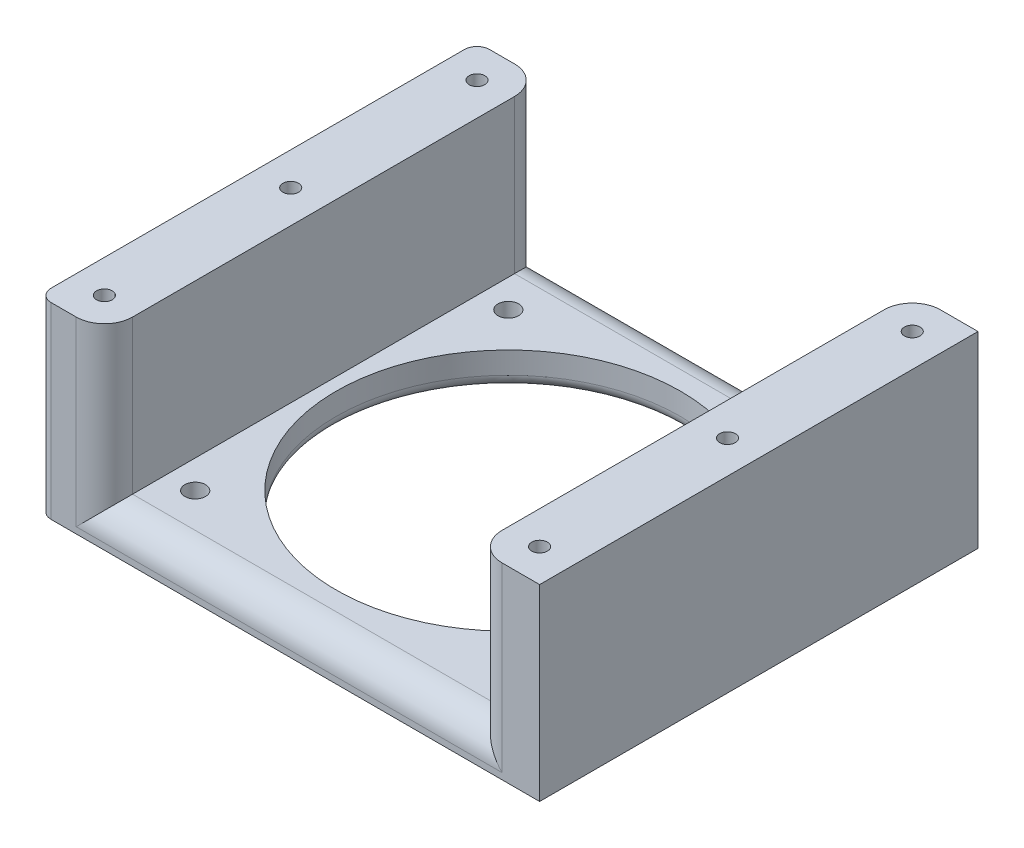
SolidWorks part; units mm, degrees
ref_plane "Front Plane" through (0, 0, 0) normal (0, 0, 1) x (1, 0, 0)
ref_plane "Top Plane" through (0, 0, 0) normal (0, 1, 0) x (1, 0, 0)
ref_plane "Right Plane" through (0, 0, 0) normal (1, 0, 0) x (0, 0, -1)
sketch "Sketch1" plane through (0, 0, 0) normal (0, 1, 0) x (1, 0, 0)
  line L1 (-42.6313, 37.6028) -> (37.3687, 37.6028)
  line L2 (-42.6313, 37.6028) -> (-42.6313, -32.3972)
  line L3 (-42.6313, -32.3972) -> (37.3687, -32.3972)
  line L4 (37.3687, 37.6028) -> (37.3687, -32.3972)
  dimension "D1" = 80
  dimension "D2" = 70
extrude "Boss-Extrude1" add sketch "Sketch1" along normal blind 35.5
sketch "Sketch2" plane through (0, 0, 32.3972) normal (0, 0, 1) x (1, 0, 0)
  line L0 (-42.6313, 35.5) -> (37.3687, 35.5) construction
  line L1 (-32.1313, 30) -> (26.8687, 30)
  line L2 (-32.1313, 30) -> (-32.1313, 5.5)
  line L3 (-32.1313, 5.5) -> (26.8687, 5.5)
  line L4 (26.8687, 30) -> (26.8687, 5.5)
  line L5 (-42.6313, 35.5) -> (-42.6313, 0) construction
  dimension "D1" = 59
  dimension "D2" = 24.5
  dimension "D3" = 5.5
  dimension "D4" = 10.5
extrude "Cut-Extrude1" cut sketch "Sketch2" against normal up to next
sketch "Sketch6" plane through (0, 0, 0) normal (0, -1, 0) x (1, 0, 0)
  line L0 (-42.6313, 32.3972) -> (37.3687, 32.3972) construction
  line L2 (-42.6313, -37.6028) -> (-42.6313, 32.3972) construction
  circle A0 centre (-2.6313, -2.6028) radius 27.5
  dimension "D3" = 55
  dimension "D1" = 35
  dimension "D2" = 40
extrude "Cut-Extrude3" cut sketch "Sketch6" against normal blind 5.5
sketch "Sketch7" plane through (0, 0, 0) normal (0, -1, 0) x (1, 0, 0)
  line L0 (-42.6313, -37.6028) -> (-42.6313, 32.3972) construction
  line L1 (-42.6313, 32.3972) -> (37.3687, 32.3972) construction
  line L2 (37.3687, 32.3972) -> (37.3687, -37.6028) construction
  line L3 (37.3687, -37.6028) -> (-42.6313, -37.6028) construction
  point P0 (-27.6313, 22.3972)
  point P1 (22.3687, 22.3972)
  point P2 (22.3687, -27.6028)
  point P3 (-27.6313, -27.6028)
  dimension "D1" = 15
  dimension "D2" = 10
  dimension "D3" = 10
  dimension "D4" = 15
  dimension "D5" = 15
  dimension "D6" = 10
  dimension "D7" = 10
  dimension "D8" = 15
hole_wizard "M4x0.7 Tapped Hole1" positions "3DSketch2" profile "Sketch8" tap size "M4x0.7" standard "Ansi Metric" end condition up to next
sketch3d "3DSketch2"
  point P0 (22.3687, 0, 22.3972)
  point P3 (22.3687, 0, -27.6028)
  point P6 (-27.6313, 0, -27.6028)
  point P9 (-27.6313, 0, 22.3972)
sketch "Sketch8" plane through (22.3687, 0, 22.3972) normal (1, 0, 0) x (0, 0, -1)
  line L0 (0, 0) -> (0, 5.5)
  line L1 (0, 5.5) -> (1.65, 5.5)
  line L2 (1.65, 5.5) -> (1.65, 0)
  line L5 (1.65, 0) -> (0, 0)
  line L11 (0, -6.35) -> (0, 107.95) construction
  dimension "Thread Major Dia." = 3.3
  dimension "Thru Tap Drill Depth" = 5.5
fillet "Fillet2" radius 2 1 edges at (-2.6313, 0, -30.1028)
sketch "Sketch9" plane through (0, 35.5, 0) normal (0, 1, 0) x (-1, 0, 0)
  line L1 (42.6313, -37.6028) -> (-37.3687, -37.6028)
  line L2 (42.6313, -37.6028) -> (42.6313, 32.3972)
  line L3 (42.6313, 32.3972) -> (-37.3687, 32.3972)
  line L4 (-37.3687, -37.6028) -> (-37.3687, 32.3972)
extrude "Cut-Extrude5" cut sketch "Sketch9" against normal up to surface (5.5 mm away) up to face at (-2.6313, 30, -2.6028)
sketch "Sketch10" plane through (0, 30, 0) normal (0, 1, 0) x (1, 0, 0)
  line L0 (-42.6313, 37.6028) -> (-32.1313, 37.6028) construction
  line L1 (-42.6313, -32.3972) -> (-42.6313, 37.6028) construction
  line L2 (-32.1313, -32.3972) -> (-42.6313, -32.3972) construction
  line L3 (26.8687, 37.6028) -> (26.8687, -32.3972) construction
  line L4 (26.8687, 37.6028) -> (37.3687, 37.6028) construction
  line L5 (37.3687, -32.3972) -> (26.8687, -32.3972) construction
  point P0 (-37.3813, 32.3528)
  point P1 (-37.3813, 2.6028)
  point P2 (-37.3813, -27.1472)
  point P3 (-37.3813, 37.6028)
  point P12 (32.1187, 32.3528)
  point P13 (32.1187, 2.8528)
  point P14 (32.1187, -27.1472)
  dimension "D1" = 5.25
  dimension "D2" = 5.25
  dimension "D3" = 5.25
  dimension "D4" = 35
  dimension "D5" = 5.25
  dimension "D6" = 5.25
  dimension "D7" = 5.25
hole_wizard "Tap Drill for M3x0.5 Tap1" positions "3DSketch3" profile "Sketch11" hole size "M3x0.5" standard "Ansi Metric"
sketch3d "3DSketch3"
  point P0 (-37.3813, 30, -32.3528)
  point P3 (-37.3813, 30, -2.6028)
  point P6 (-37.3813, 30, 27.1472)
  point P9 (32.1187, 30, -32.3528)
  point P12 (32.1187, 30, -2.8528)
  point P15 (32.1187, 30, 27.1472)
sketch "Sketch11" plane through (-37.3813, 30, -32.3528) normal (1, 0, 0) x (0, 0, 1)
  line L0 (0, 0) -> (0, 15.7511)
  line L1 (0, 15.7511) -> (1.25, 15)
  line L2 (1.25, 15) -> (1.25, 0)
  line L5 (1.25, 0) -> (0, 0)
  line L10 (0, 15.7511) -> (-1.25, 15) construction
  line L11 (0, -6.35) -> (0, 107.95) construction
  dimension "Hole Dia." = 2.5
  dimension "Hole Depth" = 15
  dimension "Drill Angle" = 118
fillet "Fillet5" radius 2 1 edges at (-42.6313, 15, 32.3972)
fillet "Fillet6" radius 2 1 edges at (-42.6313, 15, -37.6028)
fillet "Fillet7" radius 4.5 3 edges at (-32.1313, 17.75, 32.3972) (-2.6313, 5.5, 32.3972) (26.8687, 17.75, 32.3972)
fillet "Fillet8" radius 4.5 3 edges at (26.8687, 17.75, -37.6028) (-2.6313, 5.5, -37.6028) (-32.1313, 17.75, -37.6028)
sketch "Sketch13" plane through (0, 0, 0) normal (0, -1, 0) x (1, 0, 0)
  line L0 (37.3687, 32.3972) -> (37.3687, -37.6028) construction
  line L1 (-40.6313, 32.3972) -> (37.3687, 32.3972) construction
  line L2 (37.3687, -37.6028) -> (-40.6313, -37.6028) construction
  line L3 (-42.6313, -35.6028) -> (-42.6313, 30.3972) construction
  point P4 (32.6187, 12.3972)
  point P5 (32.6187, -17.6028)
  point P12 (-37.8813, 12.3972)
  point P13 (-37.8813, -17.6028)
  dimension "D1" = 4.75
  dimension "D2" = 20
  dimension "D3" = 20
  dimension "D4" = 4.75
  dimension "D5" = 4.75
  dimension "D6" = 4.75
  dimension "D7" = 20
  dimension "D8" = 20
hole_wizard "Tap Drill for M3x0.5 Tap2" positions "3DSketch4" profile "Sketch14" hole size "M3x0.5" standard "Ansi Metric"
sketch3d "3DSketch4"
  point P0 (32.6187, 0, 12.3972)
  point P3 (32.6187, 0, -17.6028)
  point P6 (-37.8813, 0, 12.3972)
  point P9 (-37.8813, 0, -17.6028)
sketch "Sketch14" plane through (32.6187, 0, 12.3972) normal (1, 0, 0) x (0, 0, -1)
  line L0 (0, 0) -> (0, 15.7511)
  line L1 (0, 15.7511) -> (1.25, 15)
  line L2 (1.25, 15) -> (1.25, 0)
  line L5 (1.25, 0) -> (0, 0)
  line L10 (0, 15.7511) -> (-1.25, 15) construction
  line L11 (0, -6.35) -> (0, 107.95) construction
  dimension "Hole Dia." = 2.5
  dimension "Hole Depth" = 15
  dimension "Drill Angle" = 118
